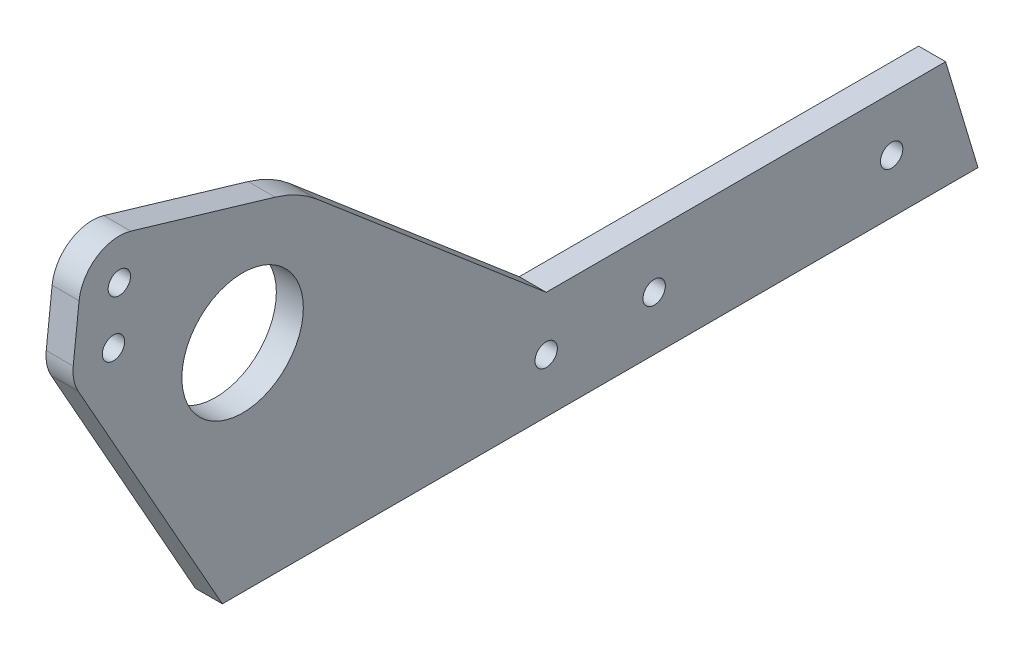
SolidWorks part; units mm, degrees
material "PC High Viscosity"
ref_plane "Front Plane" through (0, 0, 0) normal (0, 0, 1) x (1, 0, 0)
ref_plane "Top Plane" through (0, 0, 0) normal (0, 1, 0) x (1, 0, 0)
ref_plane "Right Plane" through (0, 0, 0) normal (1, 0, 0) x (0, 0, -1)
sketch "Sketch1" plane through (0, 0, 0) normal (1, 0, 0) x (0, 0, -1)
  line L0 (0, 0) -> (-84.1375, 0) construction
  line L1 (-84.1375, 0) -> (-84.1375, 38.1) construction
  line L2 (0, 0) -> (12.7, 0) construction
  line L3 (-12.7, 0) -> (-12.7, -12.7) construction
  line L4 (-88.9, -961.9) -> (-88.9, 49038.1) construction
  line L5 (-12.7, -12.7) -> (-88.9, -12.7)
  line L6 (-88.9, -12.7) -> (-122.8267, 47.5995)
  line L7 (-12.7, 0) -> (-12.7, 12.7) construction
  line L8 (-12.7, 12.7) -> (-66.6375, 58.6445)
  line L9 (-12.7, 12.7) -> (25.4, 12.7)
  line L10 (-12.7, -12.7) -> (25.4, -12.7)
  line L12 (-1084.1375, 38.1) -> (48915.8625, 38.1) construction
  line L13 (-81.8955, 38.916) -> (46902.7355, 17139.9232) construction
  line L15 (25.4, -12.7) -> (88.9, -12.7)
  line L16 (88.9, -12.7) -> (81.28, 12.7)
  line L17 (25.4, 12.7) -> (81.28, 12.7)
  line L18 (-84.1375, 0) -> (-100.0125, 0) construction
  line L19 (12.7, 0) -> (68.58, 0) construction
  line L20 (-57.3104, 35.162) -> (-84.1375, 38.1) construction
  line L21 (-84.1375, 38.1) -> (-110.9646, 41.038) construction
  line L22 (-84.1375, 38.1) -> (-77.4224, 99.4151) construction
  line L23 (-57.3104, 35.162) -> (-41.1667, 182.569) construction
  line L24 (-110.9646, 41.038) -> (-94.4503, 191.829) construction
  line L25 (-84.1375, 38.1) -> (-113.1428, 64.8947) construction
  line L26 (-84.1375, 38.1) -> (-114.5255, 52.2701) construction
  line L27 (-108.1093, 67.1095) -> (-112.5442, 70.3612) construction
  line L28 (-112.5442, 70.3612) -> (-117.5777, 68.1464) construction
  line L29 (-117.5777, 68.1464) -> (-118.1764, 62.6798) construction
  line L30 (-118.1764, 62.6798) -> (-113.7415, 59.4281) construction
  line L31 (-113.7415, 59.4281) -> (-108.708, 61.6429) construction
  line L32 (-108.708, 61.6429) -> (-108.1093, 67.1095) construction
  line L33 (-114.5255, 52.2701) -> (-123.9938, 53.3071) construction
  line L34 (-118.9603, 55.5219) -> (-119.559, 50.0553) construction
  line L35 (-119.559, 50.0553) -> (-115.1241, 46.8036) construction
  line L36 (-115.1241, 46.8036) -> (-110.0906, 49.0184) construction
  line L37 (-110.0906, 49.0184) -> (-109.4919, 54.4849) construction
  line L38 (-109.4919, 54.4849) -> (-113.9268, 57.7367) construction
  line L39 (-113.9268, 57.7367) -> (-118.9603, 55.5219) construction
  line L40 (-123.9938, 53.3071) -> (-122.6112, 65.9316)
  line L41 (-84.1375, 38.1) -> (-66.6375, 58.6445) construction
  line L43 (-110.44, 74.0281) -> (-76.4794, 63.9781)
  line L44 (-84.1375, 38.1) -> (-76.4794, 63.9781) construction
  circle A0 centre (-84.1375, 38.1) radius 14.2875
  circle A1 centre (-12.7, 0) radius 2.6289
  circle A2 centre (12.7, 0) radius 2.6289
  circle A7 centre (68.58, 0) radius 2.6289
  arc A8 (-110.9646, 41.038) -> (-57.3104, 35.162) centre (-84.1375, 38.1) ccw construction
  circle A9 centre (-113.1428, 64.8947) radius 4.7625 construction
  circle A10 centre (-113.1428, 64.8947) radius 2.6289
  circle A11 centre (-114.5255, 52.2701) radius 4.7625 construction
  circle A12 centre (-114.5255, 52.2701) radius 2.6289
  arc A13 (-122.8267, 47.5995) -> (-123.9938, 53.3071) centre (-114.5255, 52.2701) cw
  arc A14 (-122.6112, 65.9316) -> (-110.44, 74.0281) centre (-113.1428, 64.8947) cw
  arc A15 (-66.6375, 58.6445) -> (-76.4794, 63.9781) centre (-84.1375, 38.1) ccw
  point P5 (-12.7, 0)
  point P12 (136.6433, 118.4576)
  point P52 (-80.6559, 64.8947)
  point P56 (-76.3024, 63.6928)
  dimension "D3" = 28.575
  dimension "D6" = 5.2578
  dimension "D7" = 5.2578
  dimension "D9" = 25
  dimension "D14" = 12.7
  dimension "D15" = 55.88
  dimension "D18" = 5.2578
  dimension "D21" = 9.525
  dimension "D22" = 5.2578
  dimension "D23" = 9.525
  dimension "D24" = 5.2578
  dimension "D26" = 9.525
  dimension "D27" = 26.9875
  dimension "D1" = 84.1375
  dimension "D2" = 38.1
  dimension "D4" = 12.7
  dimension "D5" = 12.7
  dimension "D8" = 12.7
  dimension "D10" = 12.7
  dimension "D11" = 38.1
  dimension "D12" = 20
  dimension "D13" = 15.875
  dimension "D16" = 63.5
  dimension "D17" = 76.2
  dimension "D19" = 12.7
  dimension "D20" = 83.75
  dimension "D25" = 12.7
extrude "Boss-Extrude1" add sketch "Sketch1" along normal blind 6.35
